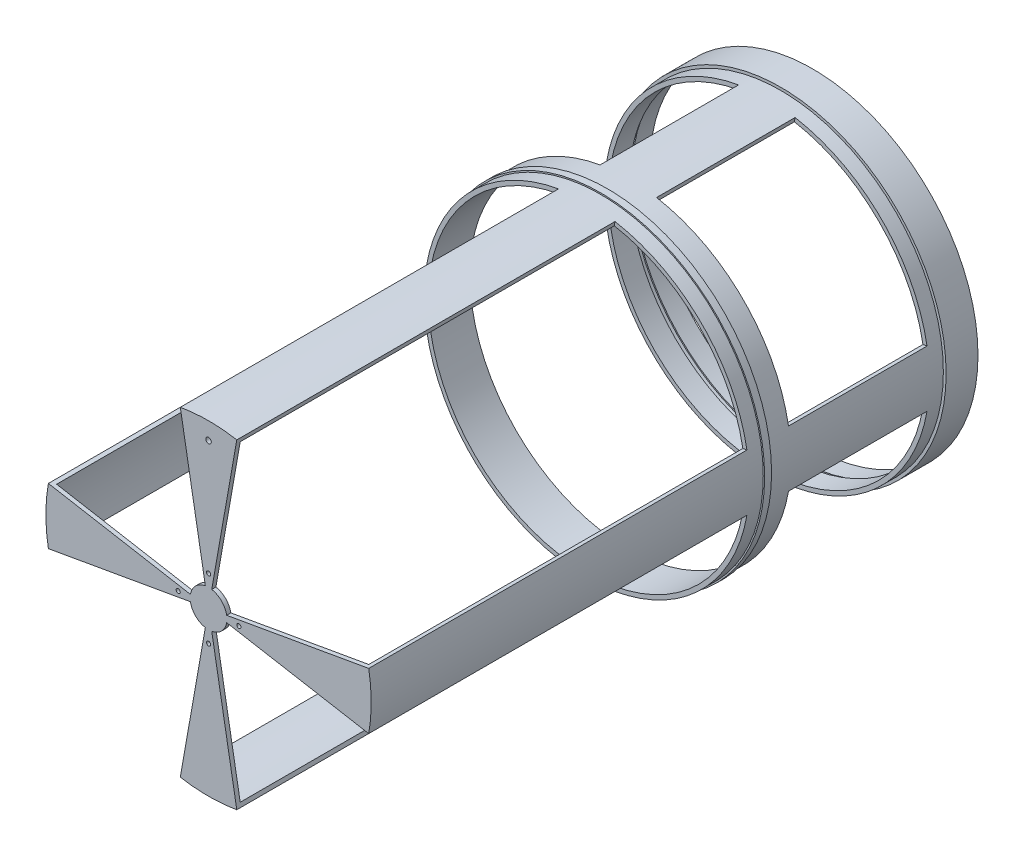
SolidWorks part; units mm, degrees
material "6063-T4"
ref_plane "Front Plane" through (0, 0, 0) normal (0, 0, 1) x (1, 0, 0)
ref_plane "Top Plane" through (0, 0, 0) normal (0, 1, 0) x (1, 0, 0)
ref_plane "Right Plane" through (0, 0, 0) normal (1, 0, 0) x (0, 0, -1)
sketch "Sketch1" plane through (0, 0, 0) normal (0, 0, 1) x (1, 0, 0)
  circle A0 centre (0, 0) radius 114.4
  circle A1 centre (0, 0) radius 119.4
extrude "Extrude1" add sketch "Sketch1" against normal blind 5
sketch "Sketch2" plane through (0, 0, -5) normal (0, 0, -1) x (-1, 0, 0)
  circle A0 centre (0, 0) radius 119.4
  circle A1 centre (0, 0) radius 118.4
extrude "Extrude2" add sketch "Sketch2" along normal blind 5
sketch "Sketch3" plane through (0, 0, -10) normal (0, 0, -1) x (-1, 0, 0)
  circle A0 centre (0, 0) radius 119.4
  circle A1 centre (0, 0) radius 117.4
extrude "Extrude3" add sketch "Sketch3" along normal blind 13
sketch "Sketch4" plane through (0, 0, 0) normal (0, 0, 1) x (1, 0, 0)
  circle A0 centre (0, 0) radius 114.4
  circle A1 centre (0, 0) radius 117.4
extrude "Extrude4" add sketch "Sketch4" along normal blind 10
sketch "Sketch5" plane through (0, 0, 10) normal (0, 0, 1) x (1, 0, 0)
  line L0 (0, 0) -> (-26.3363, 149.3606) construction
  line L1 (0, 0) -> (156.0693, 27.5192) construction
  line L2 (0, 0) -> (28.315, -160.5824) construction
  line L3 (0, 0) -> (-167.0862, -29.4618) construction
  line L4 (0, 0) -> (148.5941, -26.2012) construction
  line L5 (0, 0) -> (-30.1322, -170.8882) construction
  line L6 (0, 0) -> (-160.0063, 28.2134) construction
  line L7 (0, 0) -> (24.311, 137.8747) construction
  line L8 (20.3863, 115.6164) -> (19.8654, 112.662)
  line L9 (-20.3863, 115.6164) -> (-19.8654, 112.662)
  line L10 (115.6164, 20.3863) -> (112.662, 19.8654)
  line L11 (115.6164, -20.3863) -> (112.662, -19.8654)
  line L12 (19.8654, -112.662) -> (20.3863, -115.6164)
  line L13 (-19.8654, -112.662) -> (-20.3863, -115.6164)
  line L14 (-112.662, -19.8654) -> (-115.6164, -20.3863)
  line L15 (-112.662, 19.8654) -> (-115.6164, 20.3863)
  arc A0 (112.662, 19.8654) -> (112.662, -19.8654) centre (0, 0) cw
  circle A2 centre (0, 0) radius 114.4 construction
  arc A4 (115.6164, 20.3863) -> (115.6164, -20.3863) centre (0, 0) cw
  circle A5 centre (0, 0) radius 117.4 construction
  arc A6 (19.8654, -112.662) -> (-19.8654, -112.662) centre (0, 0) cw
  arc A7 (20.3863, -115.6164) -> (-20.3863, -115.6164) centre (0, 0) cw
  arc A8 (-112.662, -19.8654) -> (-112.662, 19.8654) centre (0, 0) cw
  arc A9 (-115.6164, -20.3863) -> (-115.6164, 20.3863) centre (0, 0) cw
  circle A10 centre (0, 0) radius 117.4 construction
  arc A11 (-19.8654, 112.662) -> (19.8654, 112.662) centre (0, 0) cw
  arc A12 (-20.3863, 115.6164) -> (20.3863, 115.6164) centre (0, 0) cw
  point P0 (0, 0)
extrude "Extrude5" add sketch "Sketch5" along normal blind 100
sketch "Sketch6" plane through (0, 0, 110) normal (0, 0, 1) x (1, 0, 0)
  circle A0 centre (0, 0) radius 114.4
  circle A1 centre (0, 0) radius 117.4
  point P0 (0, 0)
extrude "Extrude7" add sketch "Sketch6" along normal blind 15
sketch "Sketch7" plane through (0, 0, 125) normal (0, 0, 1) x (1, 0, 0)
  circle A0 centre (0, 0) radius 114.4
  circle A1 centre (0, 0) radius 118.4
  point P0 (0, 0)
extrude "Extrude8" add sketch "Sketch7" along normal blind 5
sketch "Sketch8" plane through (0, 0, 130) normal (0, 0, 1) x (1, 0, 0)
  circle A0 centre (0, 0) radius 114.4
  circle A1 centre (0, 0) radius 117.4
  point P0 (0, 0)
extrude "Extrude9" add sketch "Sketch8" along normal blind 10
sketch "Sketch9" plane through (0, 0, 140) normal (0, 0, 1) x (1, 0, 0)
  line L0 (0, 0) -> (164.537, 29.0123) construction
  line L1 (0, 0) -> (-25.7683, 146.1394) construction
  line L2 (0, 0) -> (-163.4787, -28.8257) construction
  line L3 (0, 0) -> (26.4081, -149.7676) construction
  line L4 (0, 0) -> (25.7878, 146.2502) construction
  line L5 (0, 0) -> (151.073, -26.6382) construction
  line L6 (0, 0) -> (-29.2914, -166.1196) construction
  line L7 (0, 0) -> (-217.9992, 38.4391) construction
  line L8 (-20.3863, 115.6164) -> (-19.8654, 112.662)
  line L9 (20.3863, 115.6164) -> (19.8654, 112.662)
  line L10 (112.662, 19.8654) -> (115.6164, 20.3863)
  line L11 (112.662, -19.8654) -> (115.6164, -20.3863)
  line L12 (19.8654, -112.662) -> (20.3863, -115.6164)
  line L13 (-19.8654, -112.662) -> (-20.3863, -115.6164)
  line L14 (-112.662, -19.8654) -> (-115.6164, -20.3863)
  line L15 (-112.662, 19.8654) -> (-115.6164, 20.3863)
  arc A0 (112.662, -19.8654) -> (112.662, 19.8654) centre (0, 0) ccw
  arc A1 (115.6164, -20.3863) -> (115.6164, 20.3863) centre (0, 0) ccw
  circle A2 centre (0, 0) radius 117.4 construction
  arc A3 (19.8654, -112.662) -> (-19.8654, -112.662) centre (0, 0) cw
  arc A4 (20.3863, -115.6164) -> (-20.3863, -115.6164) centre (0, 0) cw
  arc A5 (-112.662, -19.8654) -> (-112.662, 19.8654) centre (0, 0) cw
  circle A6 centre (0, 0) radius 114.4 construction
  arc A7 (-115.6164, -20.3863) -> (-115.6164, 20.3863) centre (0, 0) cw
  arc A8 (-19.8654, 112.662) -> (19.8654, 112.662) centre (0, 0) cw
  arc A9 (-20.3863, 115.6164) -> (20.3863, 115.6164) centre (0, 0) cw
  point P0 (0, 0)
extrude "Extrude10" add sketch "Sketch9" along normal blind 270
sketch "Sketch10" plane through (0, 0, 410) normal (0, 0, 1) x (1, 0, 0)
  line L0 (0, 0) -> (115.6164, 20.3863) construction
  line L1 (0, 0) -> (115.6164, -20.3863) construction
  line L2 (0, 0) -> (20.3863, -115.6164) construction
  line L3 (0, 0) -> (-20.3863, -115.6164) construction
  line L4 (0, 0) -> (-115.6164, -20.3863) construction
  line L5 (0, 0) -> (-115.6164, 20.3863) construction
  line L6 (0, 0) -> (20.3863, 115.6164) construction
  line L7 (0, 0) -> (-20.3863, 115.6164) construction
  line L8 (0, 0) -> (137.0063, 0) construction
  line L9 (0, 0) -> (0, 89.4745) construction
  line L10 (0, 0) -> (-84.9341, 0) construction
  line L11 (0, 0) -> (0, -91.1649) construction
  line L12 (13.0652, 2.3038) -> (115.6164, 20.3863)
  line L13 (13.0652, -2.3038) -> (115.6164, -20.3863)
  line L14 (2.3038, -13.0652) -> (20.3863, -115.6164)
  line L15 (-20.3863, -115.6164) -> (-2.3038, -13.0652)
  line L16 (-13.0652, -2.3038) -> (-115.6164, -20.3863)
  line L17 (-115.6164, 20.3863) -> (-13.0652, 2.3038)
  line L18 (-2.3038, 13.0652) -> (-20.3863, 115.6164)
  line L19 (20.3863, 115.6164) -> (2.3038, 13.0652)
  circle A0 centre (0, 0) radius 117.4 construction
  arc A1 (-115.6164, 20.3863) -> (-115.6164, -20.3863) centre (0, 0) ccw construction
  circle A2 centre (0, 0) radius 13.2668 construction
  circle A3 centre (21.92, 0) radius 1.5
  circle A4 centre (0, -21.92) radius 1.5
  circle A5 centre (-21.92, 0) radius 1.5
  circle A6 centre (0, 21.92) radius 1.5
  arc A7 (115.6164, 20.3863) -> (115.6164, -20.3863) centre (0, 0) cw
  arc A9 (2.3038, 13.0652) -> (13.0652, 2.3038) centre (0, 0) cw
  arc A10 (13.0652, -2.3038) -> (2.3038, -13.0652) centre (0, 0) cw
  arc A11 (-2.3038, -13.0652) -> (-13.0652, -2.3038) centre (0, 0) cw
  arc A12 (-13.0652, 2.3038) -> (-2.3038, 13.0652) centre (0, 0) cw
  arc A16 (-115.6164, -20.3863) -> (-115.6164, 20.3863) centre (0, 0) cw
  arc A18 (-20.3863, 115.6164) -> (20.3863, 115.6164) centre (0, 0) cw
  arc A19 (20.3863, 115.6164) -> (-20.3863, 115.6164) centre (0, 0) ccw construction
  arc A20 (20.3863, -115.6164) -> (-20.3863, -115.6164) centre (0, 0) cw
  circle A21 centre (0, 105.0432) radius 2
  point P0 (0, 0)
  point P26 (21.92, 0)
  point P27 (0, 21.92)
  point P29 (-21.92, 0)
  point P31 (0, -21.92)
  point P50 (0, 105.0432)
  dimension "D1" = 21.92
  dimension "D2" = 21.92
  dimension "D3" = 21.92
  dimension "D4" = 21.92
extrude "Extrude11" add sketch "Sketch10" along normal blind 3
